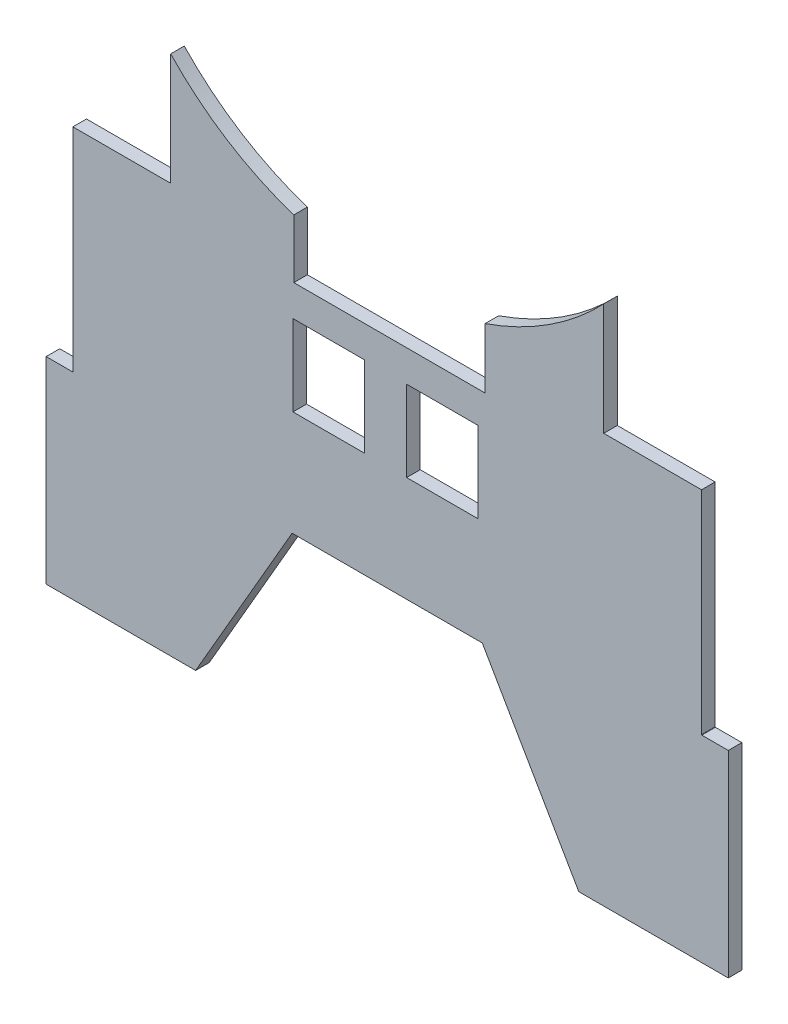
SolidWorks part; units mm, degrees
ref_plane "Front Plane" through (0, 0, 0) normal (0, 0, 1) x (1, 0, 0)
ref_plane "Top Plane" through (0, 0, 0) normal (0, 1, 0) x (1, 0, 0)
ref_plane "Right Plane" through (0, 0, 0) normal (1, 0, 0) x (0, 0, -1)
sketch "Sketch1" plane through (0, 0, 0) normal (0, 0, 1) x (1, 0, 0)
  line L0 (-91.9937, 102.7256) -> (-126.7295, 102.7256)
  line L1 (-126.7295, 102.7256) -> (-126.7462, 82.9838)
  line L2 (-126.7462, 82.9838) -> (-126.7513, 69.5502)
  line L3 (-126.7513, 69.5502) -> (-126.7516, 54.9289)
  line L4 (-126.7516, 54.9289) -> (-116.9091, 54.9289)
  line L5 (-116.9091, 54.9289) -> (-116.9091, -30.4182)
  line L6 (-116.9091, -30.4182) -> (-126.7529, -30.4182)
  line L7 (-126.7529, -30.4182) -> (-126.7529, -102.9746)
  line L8 (-126.7529, -102.9746) -> (-71.7199, -102.9746)
  line L9 (-71.7199, -102.9746) -> (-36.1992, -41.4509)
  line L10 (-36.1992, -41.4509) -> (33.8049, -41.4509)
  line L11 (33.8049, -41.4509) -> (69.3256, -102.9746)
  line L12 (69.3256, -102.9746) -> (124.3586, -102.9746)
  line L13 (124.3586, -102.9746) -> (124.3586, -30.4182)
  line L14 (124.3586, -30.4182) -> (114.6418, -30.4182)
  line L15 (114.5148, -30.2912) -> (114.5148, 54.8019)
  line L16 (114.6418, 54.9289) -> (124.3573, 54.9289)
  line L17 (124.3573, 54.9289) -> (124.357, 69.5401)
  line L18 (124.357, 69.5401) -> (124.3519, 82.9938)
  line L19 (124.3519, 82.9938) -> (124.3352, 102.7256)
  line L20 (124.3352, 102.7256) -> (89.5995, 102.7256)
  line L21 (34.8187, 60.8853) -> (34.8187, 38.7554)
  line L22 (34.8187, 38.7554) -> (-35.5817, 38.7554)
  line L23 (-35.5817, 38.7554) -> (-35.5817, 60.3343)
  arc A0 (-91.9937, 102.7256) -> (-35.5817, 60.3343) centre (-1.1971, 164.8221) ccw
  arc A1 (114.5148, -30.2912) -> (114.6418, -30.4182) centre (114.6418, -30.2912) ccw
  arc A2 (114.6418, 54.9289) -> (114.5148, 54.8019) centre (114.6418, 54.8019) ccw
  arc A3 (34.8187, 60.8853) -> (89.5995, 102.7256) centre (-1.1971, 164.8221) ccw
extrude "Boss-Extrude1" add sketch "Sketch1" along normal blind 5
sketch "Sketch2" plane through (0, 0, 5) normal (0, 0, 1) x (1, 0, 0)
  line L1 (32.3069, 27.1353) -> (5.9482, 27.1353)
  line L2 (32.3069, 27.1353) -> (32.3069, -2.6246)
  line L3 (32.3069, -2.6246) -> (5.9482, -2.6246)
  line L4 (5.9482, 27.1353) -> (5.9482, -2.6246)
  line L5 (32.3069, 27.1353) -> (5.9482, -2.6246) construction
  line L6 (32.3069, -2.6246) -> (5.9482, 27.1353) construction
  line L7 (-9.5336, 27.1353) -> (-35.8923, 27.1353)
  line L8 (-9.5336, 27.1353) -> (-9.5336, -2.6246)
  line L9 (-9.5336, -2.6246) -> (-35.8923, -2.6246)
  line L10 (-35.8923, 27.1353) -> (-35.8923, -2.6246)
  line L11 (-9.5336, 27.1353) -> (-35.8923, -2.6246) construction
  line L12 (-9.5336, -2.6246) -> (-35.8923, 27.1353) construction
  point P4 (19.1275, 12.2554)
  point P11 (-22.713, 12.2554)
extrude "Cut-Extrude1" cut sketch "Sketch2" against normal blind 5
sketch "Sketch3" plane through (0, 0, 5) normal (0, 0, 1) x (1, 0, 0)
  line L1 (-126.7295, 110.7554) -> (-91.9937, 110.7554)
  line L2 (-126.7295, 110.7554) -> (-126.7295, 102.7256)
  line L3 (-126.7295, 102.7256) -> (-91.9937, 102.7256)
  line L4 (-91.9937, 110.7554) -> (-91.9937, 102.7256)
  line L5 (-126.7295, 110.7554) -> (-91.9937, 102.7256) construction
  line L6 (-126.7295, 102.7256) -> (-91.9937, 110.7554) construction
  line L7 (89.5995, 110.7554) -> (124.3352, 110.7554)
  line L8 (89.5995, 110.7554) -> (89.5995, 102.7256)
  line L9 (89.5995, 102.7256) -> (124.3352, 102.7256)
  line L10 (124.3352, 110.7554) -> (124.3352, 102.7256)
  line L11 (89.5995, 110.7554) -> (124.3352, 102.7256) construction
  line L12 (89.5995, 102.7256) -> (124.3352, 110.7554) construction
  point P4 (-109.3616, 106.7405)
  point P11 (106.9673, 106.7405)
extrude "Boss-Extrude2" add sketch "Sketch3" against normal blind 5
sketch "Sketch4" plane through (0, 0, 5) normal (0, 0, 1) x (1, 0, 0)
  line L0 (-91.9937, 110.7554) -> (-126.7295, 110.7554) construction
  line L1 (78.5148, 47.7554) -> (133.1288, 47.7554)
  line L2 (78.5148, 47.7554) -> (78.5148, 110.7554)
  line L3 (78.5148, 110.7554) -> (133.1288, 110.7554)
  line L4 (133.1288, 47.7554) -> (133.1288, 110.7554)
  line L5 (78.5148, 47.7554) -> (133.1288, 110.7554) construction
  line L6 (78.5148, 110.7554) -> (133.1288, 47.7554) construction
  line L7 (-80.9091, 47.7554) -> (-136.2287, 47.7554)
  line L8 (-80.9091, 47.7554) -> (-80.9091, 110.7554)
  line L9 (-80.9091, 110.7554) -> (-136.2287, 110.7554)
  line L10 (-136.2287, 47.7554) -> (-136.2287, 110.7554)
  line L11 (-80.9091, 47.7554) -> (-136.2287, 110.7554) construction
  line L12 (-80.9091, 110.7554) -> (-136.2287, 47.7554) construction
  point P4 (105.8218, 79.2554)
  point P11 (-108.5689, 79.2554)
  point P15 (-126.7488, 110.7554)
  point P16 (-136.2287, 110.7554)
  point P17 (124.3352, 110.7554)
extrude "Cut-Extrude2" cut sketch "Sketch4" against normal blind 10
